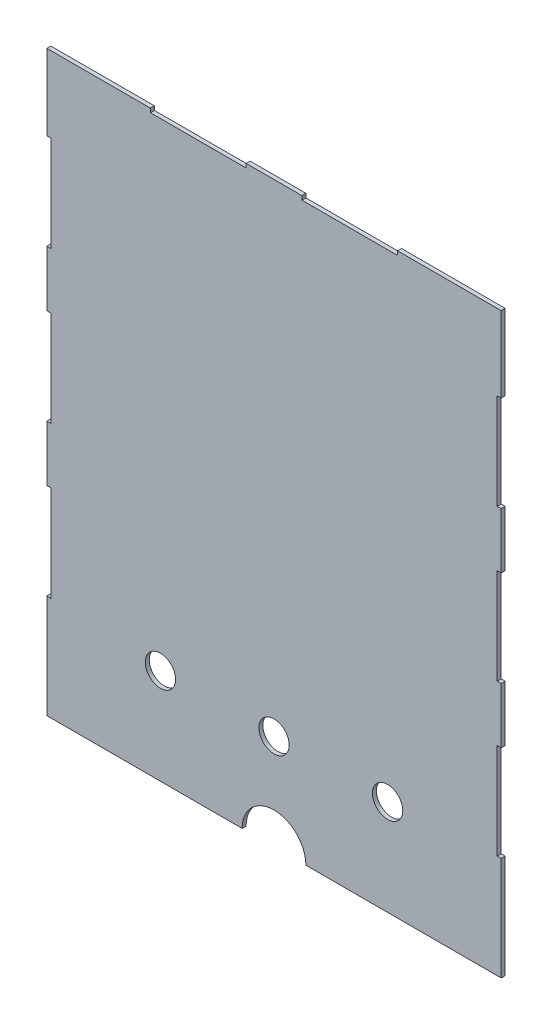
SolidWorks part; units mm, degrees
ref_plane "Front Plane" through (0, 0, 0) normal (0, 0, 1) x (1, 0, 0)
ref_plane "Top Plane" through (0, 0, 0) normal (0, 1, 0) x (1, 0, 0)
ref_plane "Right Plane" through (0, 0, 0) normal (1, 0, 0) x (0, 0, -1)
sketch "Sketch1" plane through (0, 0, 0) normal (0, 0, 1) x (1, 0, 0)
  line L1 (180.975, 0) -> (-180.975, 0)
  line L2 (180.975, 0) -> (180.975, 460.375)
  line L3 (180.975, 460.375) -> (-180.975, 460.375)
  line L4 (-180.975, 0) -> (-180.975, 460.375)
  point P4 (0, 0)
  dimension "D1" = 460.375
  dimension "D2" = 361.95
extrude "Boss-Extrude1" add sketch "Sketch1" along normal blind 3.175
sketch "Sketch2" plane through (0, 0, 3.175) normal (0, 0, 1) x (1, 0, 0)
  line L0 (180.975, 460.375) -> (-180.975, 460.375) construction
  line L1 (-98.425, 460.375) -> (-22.225, 460.375)
  line L2 (-98.425, 460.375) -> (-98.425, 457.2)
  line L3 (-98.425, 457.2) -> (-22.225, 457.2)
  line L4 (-22.225, 460.375) -> (-22.225, 457.2)
  line L5 (-180.975, 460.375) -> (-180.975, 0) construction
  line L6 (0, -47.6584) -> (0, 669.6239) construction
  line L7 (177.8, 323.85) -> (177.8, 400.05)
  line L8 (180.975, 400.05) -> (177.8, 400.05)
  line L9 (180.975, 323.85) -> (180.975, 400.05)
  line L10 (-180.975, 82.55) -> (-177.8, 82.55)
  line L11 (-180.975, 82.55) -> (-180.975, 158.75)
  line L12 (-180.975, 158.75) -> (-177.8, 158.75)
  line L13 (-177.8, 82.55) -> (-177.8, 158.75)
  line L15 (-180.975, 203.2) -> (-177.8, 203.2)
  line L16 (-180.975, 203.2) -> (-180.975, 279.4)
  line L17 (-180.975, 279.4) -> (-177.8, 279.4)
  line L18 (-177.8, 203.2) -> (-177.8, 279.4)
  line L19 (-180.975, 323.85) -> (-177.8, 323.85)
  line L20 (-180.975, 323.85) -> (-180.975, 400.05)
  line L21 (-180.975, 400.05) -> (-177.8, 400.05)
  line L22 (-177.8, 323.85) -> (-177.8, 400.05)
  line L25 (-180.975, 0) -> (180.975, 0) construction
  line L27 (180.975, 323.85) -> (177.8, 323.85)
  line L28 (177.8, 203.2) -> (177.8, 279.4)
  line L29 (180.975, 279.4) -> (177.8, 279.4)
  line L30 (180.975, 203.2) -> (180.975, 279.4)
  line L31 (180.975, 203.2) -> (177.8, 203.2)
  line L32 (177.8, 82.55) -> (177.8, 158.75)
  line L33 (180.975, 158.75) -> (177.8, 158.75)
  line L34 (180.975, 82.55) -> (180.975, 158.75)
  line L35 (180.975, 82.55) -> (177.8, 82.55)
  line L36 (22.225, 460.375) -> (22.225, 457.2)
  line L37 (98.425, 457.2) -> (22.225, 457.2)
  line L38 (98.425, 460.375) -> (98.425, 457.2)
  line L39 (98.425, 460.375) -> (22.225, 460.375)
  point P24 (-177.8, 361.95)
  point P25 (-177.8, 241.3)
  point P26 (-177.8, 120.65)
  point P29 (-60.325, 460.375)
  point P46 (60.325, 460.375)
  point P47 (177.8, 120.65)
  point P48 (177.8, 241.3)
  point P49 (177.8, 361.95)
  dimension "D1" = 3.175
  dimension "D2" = 3.175
  dimension "D3" = 3.175
  dimension "D4" = 76.2
  dimension "D5" = 76.2
  dimension "D6" = 76.2
  dimension "D7" = 120.65
  dimension "D8" = 120.65
  dimension "D9" = 120.65
  dimension "D10" = 76.2
  dimension "D13" = 3.175
  dimension "D14" = 120.65
extrude "Cut-Extrude1" cut sketch "Sketch2" against normal blind 3.175
sketch "Sketch3" plane through (0, 0, 3.175) normal (0, 0, 1) x (1, 0, 0)
  line L0 (180.975, 0) -> (180.975, 82.55) construction
  line L2 (-180.975, 0) -> (180.975, 0) construction
  line L4 (-25.4, 0) -> (25.4, 0)
  circle A0 centre (-90.4875, 76.2) radius 12.0777
  circle A1 centre (0, 76.2) radius 12.0777
  circle A2 centre (90.4875, 76.2) radius 12.0777
  arc A3 (-25.4, 0) -> (25.4, 0) centre (0, 0) cw
  dimension "D1" = 24.1554
  dimension "D2" = 24.1554
  dimension "D3" = 24.1554
  dimension "D8" = 25.4
  dimension "D4" = 90.4875
  dimension "D5" = 90.4875
  dimension "D6" = 90.4875
  dimension "D7" = 76.2
extrude "Cut-Extrude2" cut sketch "Sketch3" against normal blind 3.175
sketch "Sketch4" plane through (0, 0, 3.175) normal (0, 0, 1) x (1, 0, 0)
  line L2 (25.4, 0) -> (180.975, 0) construction
  line L3 (180.975, 0) -> (180.975, 82.55) construction
  text T0 "Derrick Cantrell" font "Century Gothic" height in points 28
  dimension "D1" = 22.86
  dimension "D2" = 120.65
equation "\"D2@Sketch3\"=\"D1@Sketch3\""
equation "\"D3@Sketch3\"=\"D1@Sketch3\""
equation "\"D5@Sketch3\"=\"D4@Sketch3\""
equation "\"D6@Sketch3\"=\"D4@Sketch3\""
